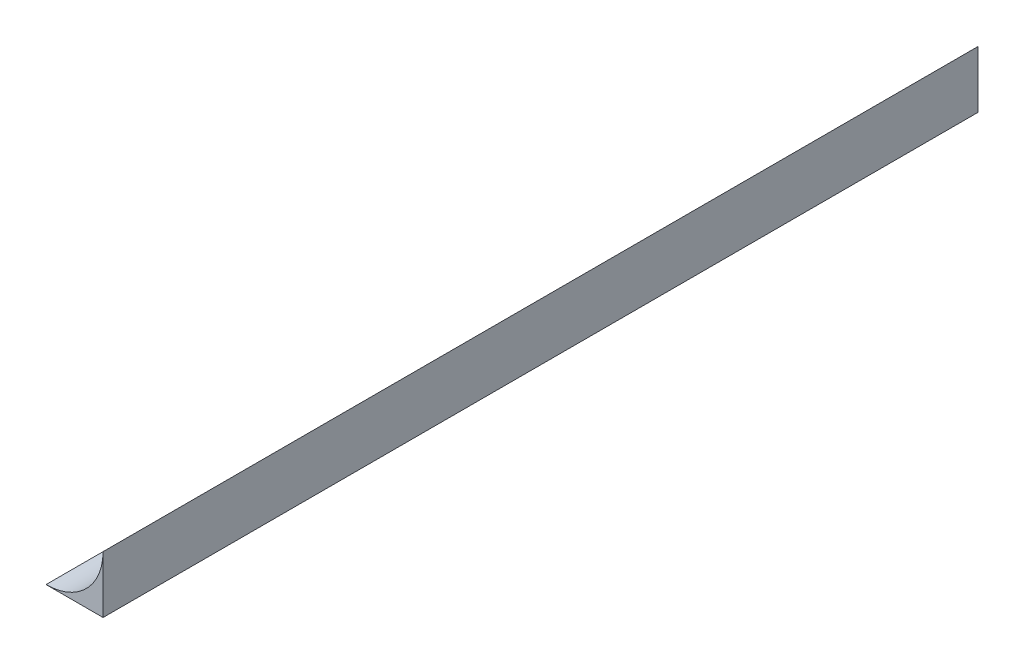
SolidWorks part; units mm, degrees
material "PLA"
ref_plane "Front Plane" through (0, 0, 0) normal (0, 0, 1) x (1, 0, 0)
ref_plane "Top Plane" through (0, 0, 0) normal (0, 1, 0) x (1, 0, 0)
ref_plane "Right Plane" through (0, 0, 0) normal (1, 0, 0) x (0, 0, -1)
sketch "Sketch1" plane through (0, 0, 0) normal (1, 0, 0) x (0, 0, -1)
  line L0 (0, 0) -> (0, 50000) construction
  line L1 (-110, 0) -> (-115, 0)
  line L2 (-110, 0) -> (-110, 110)
  line L3 (-110, 110) -> (-115, 110)
  line L4 (-115, 0) -> (-115, 110)
  line L5 (115, 0) -> (115, 110)
  line L6 (110, 110) -> (115, 110)
  line L7 (110, 0) -> (110, 110)
  line L8 (110, 0) -> (115, 0)
  dimension "D1" = 110
  dimension "D2" = 5
  dimension "D3" = 110
extrude "Boss-Extrude1" add sketch "Sketch1" along normal blind 120 and the other way blind 110
sketch "Sketch2" plane through (-110, 0, 0) normal (-1, 0, 0) x (0, 0, 1)
  line L0 (-110, 110) -> (-110, 0) construction
  line L1 (-115, 0) -> (-110, 0)
  line L2 (-115, 0) -> (-115, 37)
  line L3 (-115, 37) -> (-110, 37)
  line L4 (-110, 0) -> (-110, 37)
  line L5 (0, 0) -> (0, 50000) construction
  line L6 (110, 0) -> (110, 37)
  line L7 (115, 37) -> (110, 37)
  line L8 (115, 0) -> (115, 37)
  line L9 (115, 0) -> (110, 0)
  dimension "D1" = 37
extrude "Boss-Extrude2" add sketch "Sketch2" along normal blind 50
sketch "Sketch3" plane through (-160, 0, 0) normal (-1, 0, 0) x (0, 0, 1)
  line L5 (110, 37) -> (110, 0) construction
  line L6 (-110, 37) -> (110, 37)
  line L7 (-110, 37) -> (-110, 32)
  line L8 (-110, 32) -> (110, 32)
  line L9 (110, 37) -> (110, 32)
  dimension "D1" = 5
extrude "Boss-Extrude3" add sketch "Sketch3" against normal blind 50
sketch "Sketch4" plane through (-110, 0, 0) normal (-1, 0, 0) x (0, 0, 1)
  line L1 (-115, 110) -> (115, 110)
  line L2 (-115, 110) -> (-115, 37)
  line L3 (-115, 37) -> (115, 37)
  line L4 (115, 110) -> (115, 37)
extrude "Boss-Extrude6" add sketch "Sketch4" along normal blind 5
fillet "Fillet3" radius 15 1 edges at (-115, 37, 0)
ref_plane "Plane1" through (115, 115, 0) normal (-0.7071, -0.7071, 0) x (0, 0, 1)
sketch "Sketch9" plane through (0, 0, 115) normal (0, 0, 1) x (1, 0, 0)
  line L0 (120, 110) -> (116.4645, 106.4645)
  line L1 (116.4645, 106.4645) -> (120, 102.9289)
  line L2 (120, 110) -> (120, 0) construction
  line L3 (120, 102.9289) -> (120, 110)
  dimension "D1" = 5
  dimension "D2" = 45
extrude "Cut-Extrude3" cut sketch "Sketch9" against normal through all
sketch "Sketch5" plane through (115, 115, 0) normal (-0.7071, -0.7071, 0) x (0, 0, 1)
  line L0 (-115, -7.0711) -> (-110, -7.0711) construction
  line L1 (174, -7.0711) -> (-174, -7.0711)
  line L2 (174, -7.0711) -> (174, -234.0711)
  line L3 (174, -234.0711) -> (-174, -234.0711)
  line L4 (-174, -7.0711) -> (-174, -234.0711)
  line L6 (164, -17.0711) -> (-164, -17.0711)
  line L7 (164, -17.0711) -> (164, -224.0711)
  line L8 (164, -224.0711) -> (-164, -224.0711)
  line L9 (-164, -17.0711) -> (-164, -224.0711)
  point P8 (0, -7.0711)
  dimension "D1" = 227
  dimension "D2" = 348
  dimension "D3" = 10
  dimension "D4" = 10
  dimension "D5" = 207
  dimension "D6" = 328
extrude "Boss-Extrude7" add sketch "Sketch5" along normal blind 5 separate body
sketch "Sketch10" plane through (0, 0, 115) normal (0, 0, 1) x (1, 0, 0)
  line L0 (120, 110) -> (111.4645, 110)
  line L1 (-115, 110) -> (120, 110) construction
  line L2 (111.4645, 110) -> (111.4645, 0)
  line L3 (-160, 0) -> (120, 0) construction
  line L4 (111.4645, 0) -> (120, 0)
  line L5 (120, 0) -> (120, 102.9289)
  line L6 (276.9777, -54.0488) -> (116.4645, 106.4645) construction
  line L7 (120, 102.9289) -> (120, 0) construction
  line L8 (120, 102.9289) -> (116.4645, 106.4645)
  line L9 (116.4645, 106.4645) -> (120, 110)
  dimension "D1" = 5
extrude "Boss-Extrude8" add sketch "Sketch10" along normal blind 59
mirror "Mirror3" about plane through (0, 0, 0) normal (0, 0, 1) of "Boss-Extrude8"
fillet "Fillet5" radius 15 2 edges at (111.4645, 55, -115) (111.4645, 55, 115)
sketch "Sketch12" plane through (0, 0, 174) normal (0, 0, 1) x (1, 0, 0)
  line L0 (120, 0) -> (222.9289, 0)
  line L1 (276.9777, -54.0488) -> (116.4645, 106.4645) construction
  line L2 (222.9289, 0) -> (120, 102.9289)
  line L3 (120, 102.9289) -> (120, 0)
extrude "Boss-Extrude9" add sketch "Sketch12" against normal blind 5 separate body
sketch "Sketch13" plane through (0, 0, -174) normal (0, 0, -1) x (-1, 0, 0)
  line L0 (-120, 102.9289) -> (-120, 0)
  line L1 (-120, 0) -> (-222.9289, 0)
  line L2 (-116.4645, 106.4645) -> (-276.9777, -54.0488) construction
  line L3 (-120, 0) -> (-222.9289, 0) construction
  line L4 (-222.9289, 0) -> (-120, 102.9289)
extrude "Boss-Extrude10" add sketch "Sketch13" against normal blind 5 separate body
fillet "Fillet6" radius 3 2 edges at (111.4645, 55, 174) (111.4645, 55, -174)
sketch "Sketch14" plane through (0, 0, 115) normal (0, 0, 1) x (1, 0, 0)
  line L0 (-130, 37) -> (-115, 37)
  line L1 (-115, 37) -> (-115, 120.1636)
  line L2 (-115, 120.1636) -> (321.9949, 120.1636)
  line L3 (321.9949, 120.1636) -> (321.9949, -84.0108)
  line L4 (321.9949, -84.0108) -> (-160, -84.0108)
  line L5 (-160, -84.0108) -> (-160, 37)
  line L6 (-160, 37) -> (-130, 37)
extrude "Cut-Extrude4" cut sketch "Sketch14" against normal through all both and the other way through all
sketch "Sketch15" plane through (0, 37, 0) normal (0, -1, 0) x (1, 0, 0)
  line L0 (-115, 0) -> (-50115, 0) construction
  line L1 (-115, -115) -> (-115, 115) construction
  circle A0 centre (-121, -70) radius 1.2
  circle A1 centre (-121, 70) radius 1.2
  point P4 (-115, 0)
  dimension "D1" = 2.4
  dimension "D2" = 70
  dimension "D3" = 6
extrude "Cut-Extrude5" cut sketch "Sketch15" against normal through all
ref_plane "Plane2" through (0, 47, 0) normal (0, -1, 0) x (-1, 0, 0)
sketch "Sketch18" plane through (0, 47, 0) normal (0, -1, 0) x (-1, 0, 0)
  line L0 (115, 0) -> (50115, 0) construction
  line L1 (115, 115) -> (115, -115) construction
  circle A0 centre (121, 70) radius 3
  circle A1 centre (121, -70) radius 3
  point P7 (115, 0)
  dimension "D1" = 6
extrude "Cut-Extrude6" cut sketch "Sketch18" along normal blind 9
